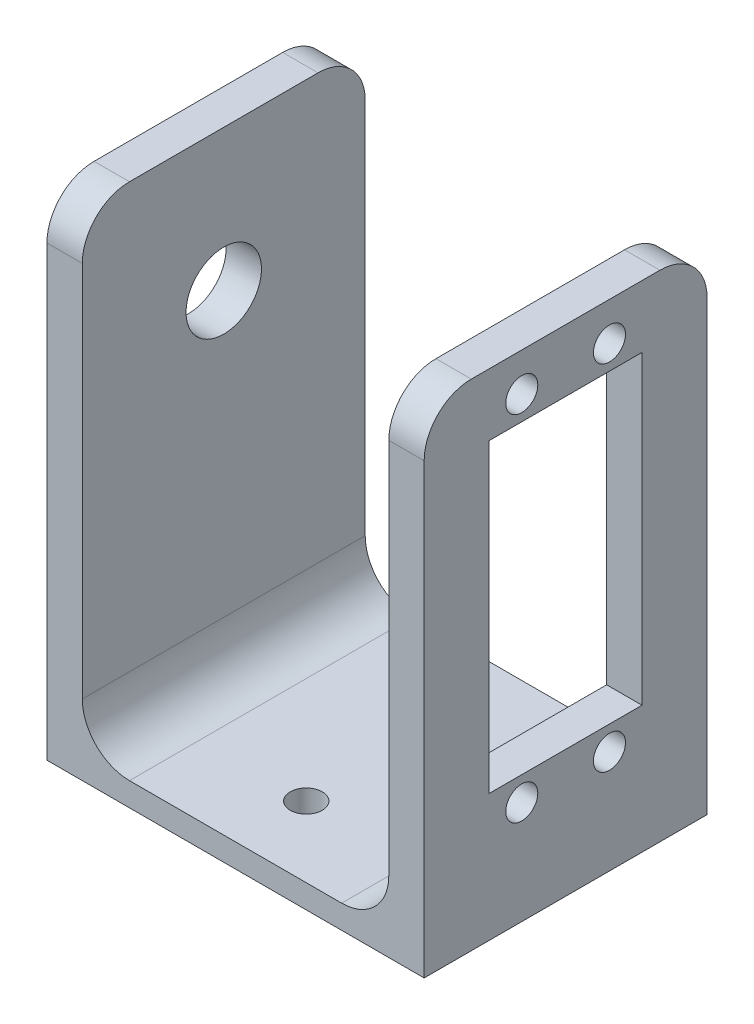
SolidWorks part; units mm, degrees
material "ABS"
ref_plane "Front" through (0, 0, 0) normal (0, 0, 1) x (1, 0, 0)
ref_plane "Top" through (0, 0, 0) normal (0, 1, 0) x (1, 0, 0)
ref_plane "Right" through (0, 0, 0) normal (1, 0, 0) x (0, 0, -1)
sketch "Sketch1" plane through (0, 0, 0) normal (0, 1, 0) x (1, 0, 0)
  line L1 (0, 0) -> (50.8, 0)
  line L2 (0, 0) -> (0, 38.1)
  line L3 (0, 38.1) -> (50.8, 38.1)
  line L4 (50.8, 0) -> (50.8, 38.1)
  dimension "D1" = 38.1
  dimension "D2" = 50.8
extrude "Boss-Extrude1" add sketch "Sketch1" along normal blind 3.175
sketch "Sketch2" plane through (0, 3.175, 0) normal (0, 1, 0) x (1, 0, 0)
  line L0 (0, 0) -> (50.8, 0) construction
  line L1 (50.8, 38.1) -> (46.0375, 38.1)
  line L2 (50.8, 38.1) -> (50.8, 0)
  line L3 (50.8, 0) -> (46.0375, 0)
  line L4 (46.0375, 38.1) -> (46.0375, 0)
  line L5 (50.8, 38.1) -> (0, 38.1) construction
  line L6 (4.7625, 38.1) -> (0, 38.1)
  line L7 (4.7625, 38.1) -> (4.7625, 0)
  line L8 (4.7625, 0) -> (0, 0)
  line L9 (0, 38.1) -> (0, 0)
  dimension "D1" = 4.7625
extrude "Boss-Extrude2" add sketch "Sketch2" along normal blind 63.5
fillet "Fillet1" radius 6.35 6 edges at (4.7625, 3.175, -19.05) (46.0375, 3.175, -19.05) (48.4187, 66.675, 0) (48.4187, 66.675, -38.1) (2.3813, 66.675, -38.1) (2.3813, 66.675, 0)
sketch "Sketch3" plane through (50.8, 0, 0) normal (1, 0, 0) x (0, 0, -1)
  line L1 (38.1, 60.325) -> (38.1, 0) construction
  line L2 (6.35, 66.675) -> (31.75, 66.675) construction
  line L5 (8.763, 58.293) -> (29.337, 58.293)
  line L6 (8.763, 58.293) -> (8.763, 17.145)
  line L7 (8.763, 17.145) -> (29.337, 17.145)
  line L8 (29.337, 58.293) -> (29.337, 17.145)
  point P0 (19.05, 10.3505)
  point P8 (19.05, 65.0875)
  point P9 (19.05, 66.675)
  point P14 (19.05, 17.145)
  point P15 (29.337, 37.719)
  point P16 (28.8925, 37.719)
  line B0 (28.8925, 65.0875) -> (28.8925, 10.3505) construction
  line B1 (28.8925, 65.0875) -> (9.2075, 65.0875) construction
  line B2 (9.2075, 65.0875) -> (9.2075, 10.3505) construction
  circle B3 centre (24.9555, 61.5315) radius 2.159
  circle B4 centre (13.1445, 61.5315) radius 2.159
  circle B5 centre (13.1445, 13.9065) radius 2.159
  circle B6 centre (24.9555, 13.9065) radius 2.159
  dimension "D1" = 1.5875
  dimension "D2" = 41.148
  dimension "D3" = 20.574
sketch_block_instance "ServoMountingHoles-1"
sketch_block "ServoMountingHoles"
extrude "Cut-Extrude1" cut sketch "Sketch3" against normal up to next
sketch "Sketch4" plane through (0, 3.175, 0) normal (0, 1, 0) x (1, 0, 0)
  line L0 (25.4, 28.575) -> (25.4, 9.525) construction
  line L1 (11.1125, 19.05) -> (39.6875, 19.05) construction
  line L2 (11.1125, 38.1) -> (11.1125, 0) construction
  line L3 (39.6875, 0) -> (39.6875, 38.1) construction
  circle A0 centre (25.4, 28.575) radius 2.159
  circle A1 centre (25.4, 9.525) radius 2.159
  point P10 (25.4, 19.05)
  dimension "D1" = 19.05
  dimension "D2" = 4.318
extrude "Cut-Extrude2" cut sketch "Sketch4" against normal up to next
sketch "Sketch5" plane through (0, 0, 0) normal (-1, 0, 0) x (0, 0, 1)
  line L0 (-31.75, 66.675) -> (-6.35, 66.675) construction
  circle A0 centre (-19.05, 47.625) radius 5.08
  point P4 (-19.05, 66.675)
  dimension "D1" = 19.05
extrude "Cut-Extrude3" cut sketch "Sketch5" against normal up to next
